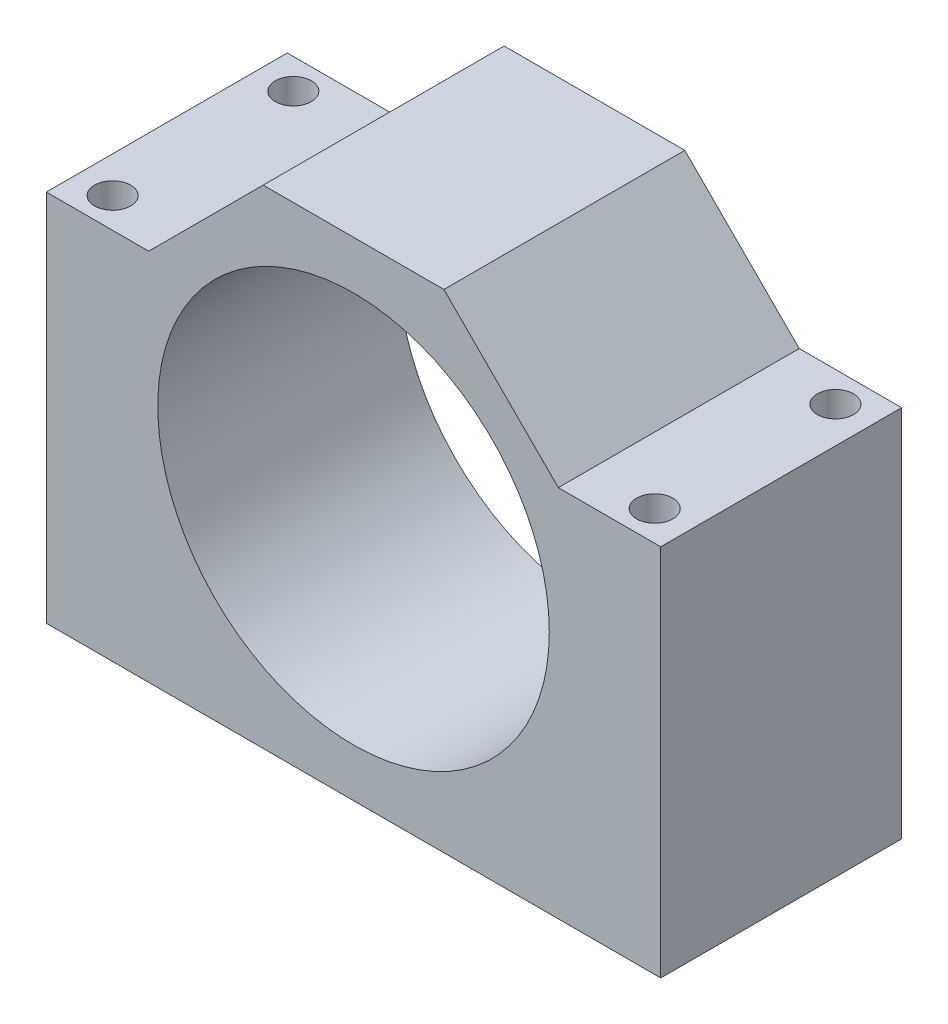
SolidWorks part; units mm, degrees
ref_plane "Front Plane" through (0, 0, 0) normal (0, 0, 1) x (1, 0, 0)
ref_plane "Top Plane" through (0, 0, 0) normal (0, 1, 0) x (1, 0, 0)
ref_plane "Right Plane" through (0, 0, 0) normal (1, 0, 0) x (0, 0, -1)
sketch "Sketch1" plane through (0, 0, 0) normal (0, 0, 1) x (1, 0, 0)
  line L0 (0, 0) -> (102, 0)
  line L1 (0, 0) -> (0, 62)
  line L2 (0, 62) -> (17, 62)
  line L3 (17, 62) -> (36, 81)
  line L4 (36, 81) -> (66, 81)
  line L5 (51, 79.2142) -> (51, 0) construction
  line L6 (51, 81) -> (51, 73) construction
  line L8 (51, 8) -> (51, 0) construction
  line L9 (85, 62) -> (66, 81)
  line L10 (102, 62) -> (85, 62)
  line L11 (102, 0) -> (102, 62)
  circle A0 centre (51, 40.5) radius 32.5
  point P13 (0, 0)
  dimension "D7" = 65
  dimension "D1" = 51
  dimension "D2" = 62
  dimension "D3" = 15
  dimension "D4" = 17
  dimension "D5" = 8
  dimension "D6" = 8
extrude "Boss-Extrude1" add sketch "Sketch1" along normal blind 40
sketch "Sketch2" plane through (0, 62, 0) normal (0, 1, 0) x (1, 0, 0)
  line L1 (102, -40) -> (0, -40) construction
  line L2 (102, -40) -> (102, 0) construction
  line L3 (102, 0) -> (0, 0) construction
  line L4 (0, -40) -> (0, 0) construction
  line L5 (102, -40) -> (0, 0) construction
  line L6 (102, 0) -> (0, -40) construction
  line L11 (96, -35) -> (6, -35) construction
  line L12 (96, -35) -> (96, -5) construction
  line L13 (96, -5) -> (6, -5) construction
  line L14 (6, -35) -> (6, -5) construction
  line L15 (96, -35) -> (6, -5) construction
  line L16 (96, -5) -> (6, -35) construction
  circle A0 centre (6, -5) radius 3
  circle A1 centre (6, -35) radius 3
  circle A2 centre (96, -5) radius 3
  circle A3 centre (96, -35) radius 3
  point P0 (51, -20)
  point P8 (51, -20)
  dimension "D3" = 6
  dimension "D1" = 90
  dimension "D2" = 30
extrude "Cut-Extrude1" cut sketch "Sketch2" against normal through all
